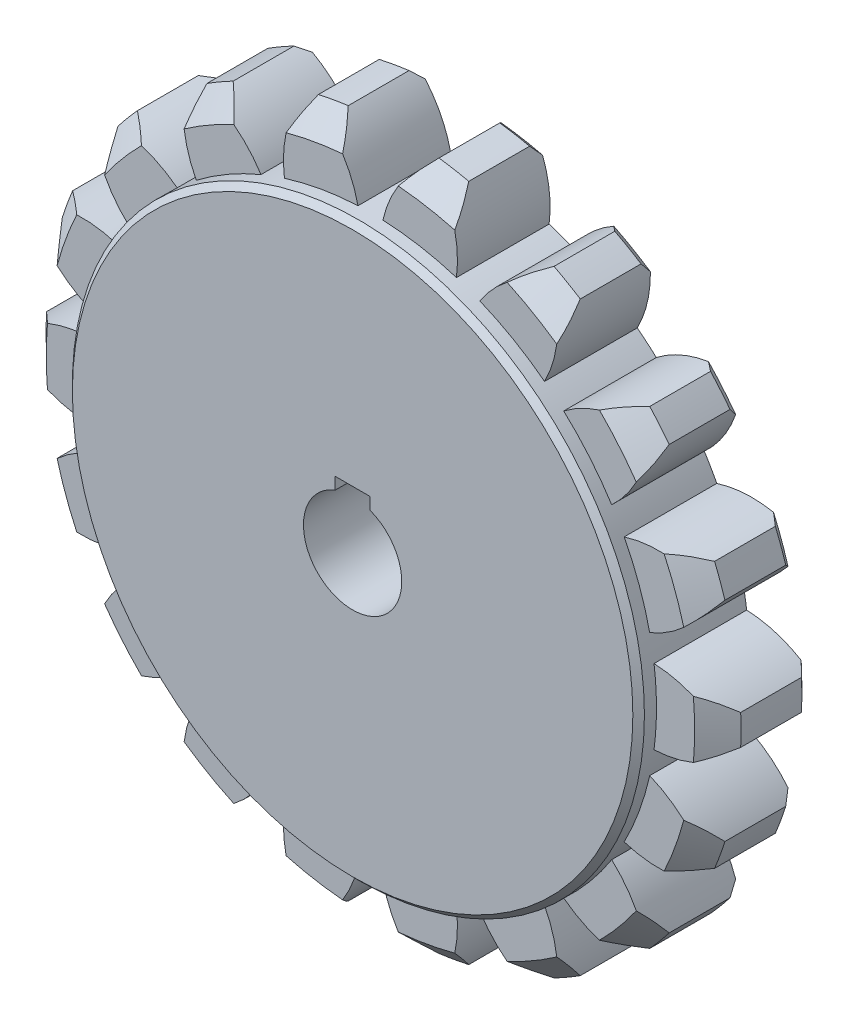
SolidWorks part; units mm, degrees
extrude "Gear Blank" add sketch "Sketch1" along normal mid plane 8
sketch "Sketch1" plane through (0, 0, 0) normal (0, 0, 1) x (1, 0, 0)
  circle A0 centre (0, 0) radius 30
  dimension "D1" = 60
chamfer "Front Gear Chamfer" distance 2 angle 45 1 edges at (30, 0, 4)
ref_plane "Plane1" through (0, 0, 0) normal (0, 0, 1) x (1, 0, 0)
ref_plane "Plane2" through (0, 0, 0) normal (0, 1, 0) x (-1, 0, 0)
ref_plane "Plane3" through (0, 0, 0) normal (1, 0, 0) x (0, 0, -1)
chamfer "Rear Gear Chamfer" distance 0.75 angle 45 1 edges at (30, 0, -4)
sketch "Sketch2" plane through (0, 0, 0) normal (0, 0, 1) x (1, 0, 0)
  line L0 (0, 30) -> (0, 0) construction
  line L1 (0, 0) -> (9.6524, 0) construction
  line L2 (0, 0) -> (-3.9158, 29.7433) construction
  line L3 (0, 0) -> (3.9158, 29.7433) construction
  line L4 (0, 0) -> (1.0774, 24.6765) construction
  line L5 (0, 0) -> (-1.0774, 24.6765) construction
  arc A1 (3.9158, 29.7433) -> (-3.9158, 29.7433) centre (0, 0) ccw
  arc A2 (3.9158, 29.7433) -> (1.0774, 24.6765) centre (10.845, 22.5332) ccw
  arc A3 (-3.9158, 29.7433) -> (-1.0774, 24.6765) centre (-10.845, 22.5332) cw
  arc A4 (-1.0774, 24.6765) -> (1.0774, 24.6765) centre (0, 0) cw
  circle A5 centre (0, 0) radius 30 construction
  dimension "D2" = 10
  dimension "D1" = 49.4
extrude "Tooth Cut" cut sketch "Sketch2" against normal mid plane 8
pattern_circular "Tooth Copies" count 18 over 360 about axis through (0, 0, 0) along (0, 0, 1) of "Tooth Cut"
sketch "Sketch3" plane through (0, 0, 4) normal (0, 0, 1) x (1, 0, 0)
  circle A0 centre (0, 0) radius 24.7
  arc A1 (7.4274, -23.5568) -> (9.4523, -22.8198) centre (0, 0) ccw construction
extrude "Boss-Extrude1" add sketch "Sketch3" along normal blind 1.54
chamfer "Chamfer1" distance 0.5 angle 45 1 edges at (24.7, 0, 5.54)
sketch "Sketch4" plane through (0, 0, -4) normal (0, 0, -1) x (-1, 0, 0)
  line L0 (0, 0) -> (0, 5) construction
  line L1 (0, 5) -> (-1.5, 5)
  line L2 (-1.5, 5) -> (-1.5, 3.9686)
  line L3 (0, 5) -> (1.5, 5)
  line L4 (1.5, 5) -> (1.5, 3.9686)
  arc A0 (-1.5, 3.9686) -> (1.5, 3.9686) centre (0, 0) ccw
  dimension "D1" = 5
  dimension "D2" = 3
  dimension "D3" = 1.5
extrude "Cut-Extrude1" cut sketch "Sketch4" against normal blind 10
equation "\"D2@Tooth Copies\"=360/\"D1@Tooth Copies\""
equation "\"D4@Sketch2\" = (3/4) * \"D2@Tooth Copies\""
equation "\"D5@Sketch2\"= \"D2@Tooth Copies\" - \"D4@Sketch2\""
equation "\"D1@Sketch2\" = \"D1@Sketch1\" - 10.6"
equation "\"D1@Tooth Cut\" = \"D1@Gear Blank\""
